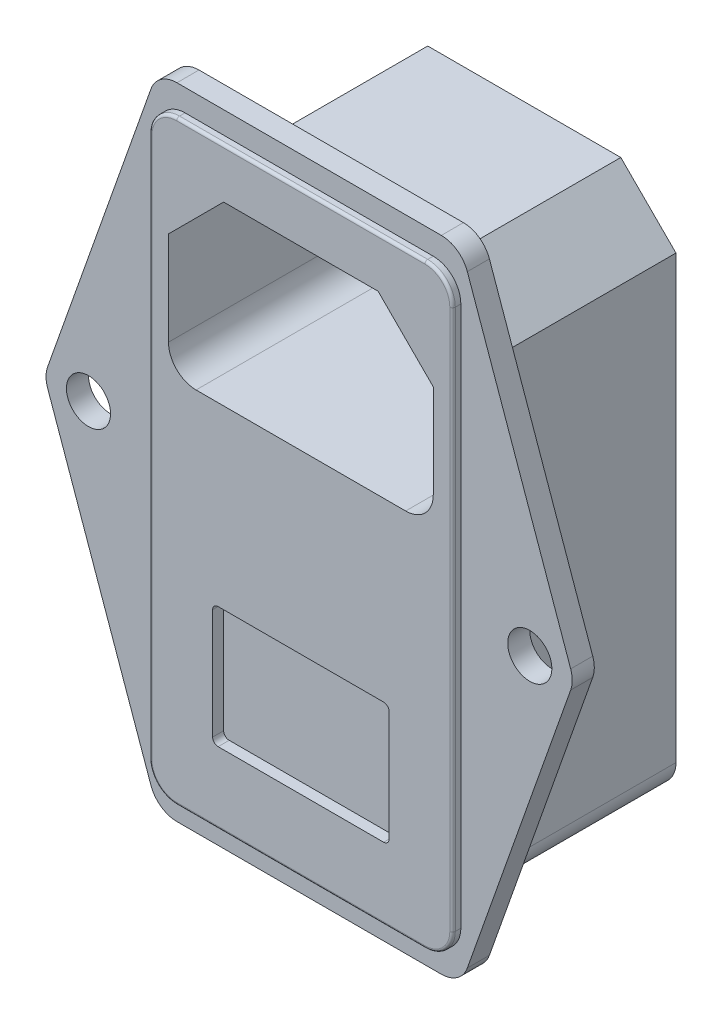
SolidWorks part; units mm, degrees
ref_plane "Front Plane" through (0, 0, 0) normal (0, 0, 1) x (1, 0, 0)
ref_plane "Top Plane" through (0, 0, 0) normal (0, 1, 0) x (1, 0, 0)
ref_plane "Right Plane" through (0, 0, 0) normal (1, 0, 0) x (0, 0, -1)
sketch "Sketch1" plane through (0, 0, 0) normal (0, 0, 1) x (1, 0, 0)
  line L0 (28.0892, 56.3331) -> (37.4555, 29.8331)
  line L1 (1.7679, 0) -> (25.7321, 0)
  line L2 (0, 0) -> (0, 58) construction
  line L3 (1.7679, 58) -> (25.7321, 58)
  line L4 (27.5, 0) -> (27.5, 58) construction
  line L5 (0, 0) -> (27.5, 58) construction
  line L6 (0, 58) -> (27.5, 0) construction
  line L7 (37.4555, 28.1669) -> (28.0892, 1.6669)
  line L8 (-0.5892, 1.6669) -> (-9.9555, 28.1669)
  line L9 (-9.9555, 29.8331) -> (-0.5892, 56.3331)
  circle A0 centre (-6.25, 29) radius 2
  circle A1 centre (33.75, 29) radius 2
  arc A2 (25.7321, 0) -> (28.0892, 1.6669) centre (25.7321, 2.5) ccw
  arc A3 (1.7679, 0) -> (-0.5892, 1.6669) centre (1.7679, 2.5) cw
  arc A4 (1.7679, 58) -> (-0.5892, 56.3331) centre (1.7679, 55.5) ccw
  arc A5 (28.0892, 56.3331) -> (25.7321, 58) centre (25.7321, 55.5) ccw
  arc A6 (37.4555, 29.8331) -> (37.4555, 28.1669) centre (35.0984, 29) cw
  arc A7 (-9.9555, 28.1669) -> (-9.9555, 29.8331) centre (-7.5984, 29) cw
  point P4 (13.75, 29)
  point P33 (37.75, 29)
  point P36 (-10.25, 29)
  dimension "D5" = 4
  dimension "D8" = 2.5
  dimension "D1" = 40
  dimension "D2" = 4
  dimension "D3" = 4
  dimension "D4" = 58
  dimension "D6" = 20
  dimension "D7" = 27.5
extrude "Boss-Extrude1" add sketch "Sketch1" along normal blind 2 contours L8 A7 L9 A4 L3 A5 L0 A6 L7 A2 L1 A3
sketch "Sketch2" plane through (0, 0, 2) normal (0, 0, 1) x (1, 0, 0)
  line L0 (1.7679, 0) -> (25.7321, 0) construction
  line L1 (2.5, 2) -> (25, 2)
  line L2 (0, 4.5) -> (0, 53.5)
  line L3 (2.5, 56) -> (25, 56)
  line L4 (27.5, 4.5) -> (27.5, 53.5)
  line L5 (0, 2) -> (27.5, 56) construction
  line L6 (0, 56) -> (27.5, 2) construction
  line L7 (25.7321, 58) -> (1.7679, 58) construction
  line L8 (1.7679, 0) -> (25.7321, 0) construction
  line L9 (25.7321, 58) -> (1.7679, 58) construction
  circle A0 centre (33.75, 29) radius 2 construction
  circle A1 centre (-6.25, 29) radius 2 construction
  circle A2 centre (33.75, 29) radius 2 construction
  circle A3 centre (-6.25, 29) radius 2 construction
  arc A4 (0, 4.5) -> (2.5, 2) centre (2.5, 4.5) ccw
  arc A5 (25, 2) -> (27.5, 4.5) centre (25, 4.5) ccw
  arc A6 (27.5, 53.5) -> (25, 56) centre (25, 53.5) ccw
  arc A7 (2.5, 56) -> (0, 53.5) centre (2.5, 53.5) ccw
  point P4 (13.75, 29)
  point P16 (13.75, 58)
  dimension "D3" = 2.5
  dimension "D1" = 27.5
  dimension "D2" = 54
extrude "Boss-Extrude2" add sketch "Sketch2" along normal blind 0.75
fillet "Fillet1" radius 0.25 8 edges at (0, 29, 2.75) (0.7322, 55.2678, 2.75) (13.75, 56, 2.75) (26.7678, 55.2678, 2.75) (27.5, 29, 2.75) (26.7678, 2.7322, 2.75) (13.75, 2, 2.75) (0.7322, 2.7322, 2.75)
sketch "Sketch3" plane through (0, 0, 0) normal (0, 0, -1) x (-1, 0, 0)
  line L0 (-27.5, 47.75) -> (-22.5, 52.75)
  line L1 (-22.5, 52.75) -> (-5, 52.75)
  line L2 (-27.5, 47.75) -> (-27.5, 7.75)
  line L3 (-25, 5.25) -> (-2.5, 5.25)
  line L4 (0, 47.75) -> (0, 7.75)
  line L5 (-27.5, 52.75) -> (0, 5.25) construction
  line L6 (-27.5, 5.25) -> (0, 52.75) construction
  line L7 (0, 47.75) -> (-5, 52.75)
  line L8 (-25.7321, 58) -> (-1.7679, 58) construction
  line L9 (-1.7679, 0) -> (-25.7321, 0) construction
  line L10 (-25.7321, 58) -> (-1.7679, 58) construction
  line L11 (-1.7679, 0) -> (-25.7321, 0) construction
  line L12 (-25, 5.25) -> (-27.5, 5.25) construction
  line L13 (-27.5, 5.25) -> (-27.5, 7.75) construction
  line L14 (-27.5, 47.75) -> (-27.5, 52.75) construction
  line L15 (-27.5, 52.75) -> (-22.5, 52.75) construction
  line L16 (-5, 52.75) -> (0, 52.75) construction
  line L17 (0, 52.75) -> (0, 47.75) construction
  arc A0 (0, 7.75) -> (-2.5, 5.25) centre (-2.5, 7.75) cw
  arc A1 (-25, 5.25) -> (-27.5, 7.75) centre (-25, 7.75) cw
  circle A2 centre (6.25, 29) radius 2 construction
  circle A3 centre (-33.75, 29) radius 2 construction
  circle A4 centre (6.25, 29) radius 2 construction
  circle A5 centre (-33.75, 29) radius 2 construction
  point P4 (-13.75, 29)
  point P26 (-13.75, 0)
  dimension "D7" = 2.5
  dimension "D1" = 27.5
  dimension "D2" = 47.5
  dimension "D3" = 5
  dimension "D4" = 5
  dimension "D5" = 5
  dimension "D6" = 5
extrude "Boss-Extrude3" add sketch "Sketch3" along normal blind 17.5
sketch "Sketch4" plane through (0, 0, 2.75) normal (0, 0, 1) x (1, 0, 0)
  line L0 (1.75, 46.5) -> (6.75, 51.5)
  line L1 (1.75, 46.5) -> (25.75, 46.5) construction
  line L2 (1.75, 46.5) -> (1.75, 38)
  line L3 (4.25, 35.5) -> (23.25, 35.5)
  line L4 (25.75, 46.5) -> (25.75, 38)
  line L5 (1.75, 46.5) -> (25.75, 35.5) construction
  line L6 (1.75, 35.5) -> (25.75, 46.5) construction
  line L7 (6.75, 51.5) -> (20.75, 51.5)
  line L8 (20.75, 51.5) -> (25.75, 46.5)
  circle A0 centre (-6.25, 29) radius 2 construction
  circle A1 centre (33.75, 29) radius 2 construction
  arc A2 (1.75, 38) -> (4.25, 35.5) centre (4.25, 38) ccw
  arc A3 (25.75, 38) -> (23.25, 35.5) centre (23.25, 38) cw
  point P4 (13.75, 41)
  point P5 (25.75, 42.25)
  point P8 (13.75, 51.5)
  dimension "D5" = 6.5
  dimension "D7" = 2.5
  dimension "D1" = 24
  dimension "D2" = 16
  dimension "D3" = 5
  dimension "D4" = 5
  dimension "D6" = 20
extrude "Cut-Extrude1" cut sketch "Sketch4" against normal blind 17.5
sketch "Sketch5" plane through (0, 0, 2.75) normal (0, 0, 1) x (1, 0, 0)
  line L0 (4.25, 35.5) -> (23.25, 35.5) construction
  line L1 (6.25, 19.5) -> (21.25, 19.5)
  line L2 (5.75, 19) -> (5.75, 9)
  line L3 (6.25, 8.5) -> (21.25, 8.5)
  line L4 (21.75, 19) -> (21.75, 9)
  line L5 (5.75, 19.5) -> (21.75, 8.5) construction
  line L6 (5.75, 8.5) -> (21.75, 19.5) construction
  circle A0 centre (33.75, 29) radius 2 construction
  arc A1 (5.75, 9) -> (6.25, 8.5) centre (6.25, 9) ccw
  arc A2 (21.25, 8.5) -> (21.75, 9) centre (21.25, 9) ccw
  arc A3 (21.75, 19) -> (21.25, 19.5) centre (21.25, 19) ccw
  arc A4 (6.25, 19.5) -> (5.75, 19) centre (6.25, 19) ccw
  point P4 (13.75, 14)
  point P10 (13.75, 35.5)
  dimension "D3" = 15
  dimension "D4" = 0.5
  dimension "D1" = 16
  dimension "D2" = 11
extrude "Cut-Extrude2" cut sketch "Sketch5" against normal blind 1 contours L2 A1 L3 A2 L4 A3 L1 A4
